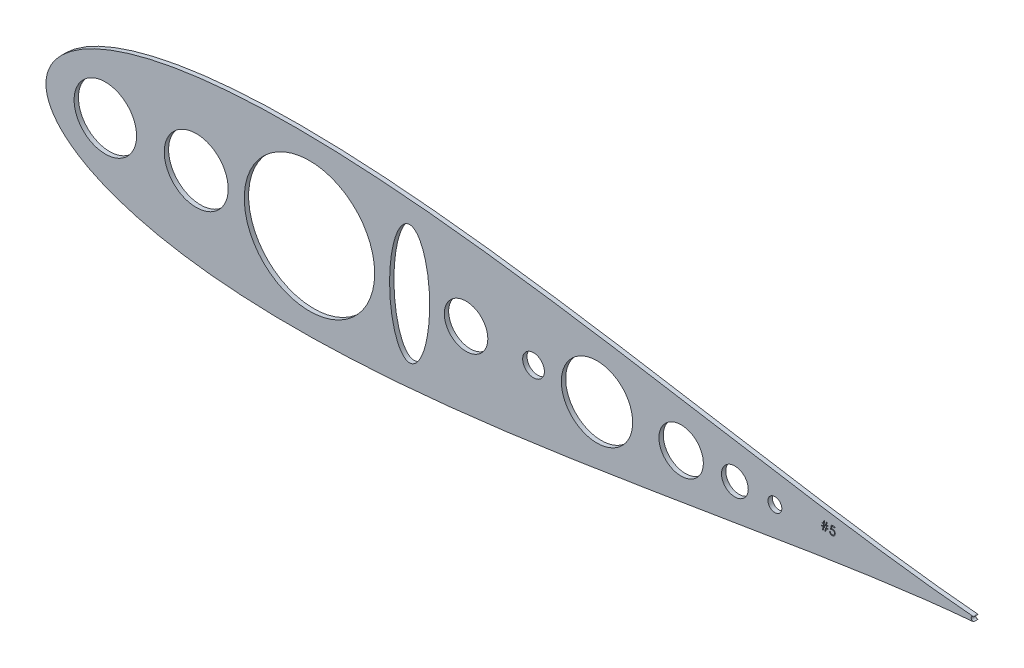
SolidWorks part; units mm, degrees
ref_plane "Front Plane" through (0, 0, 0) normal (0, 0, 1) x (1, 0, 0)
ref_plane "Top Plane" through (0, 0, 0) normal (0, 1, 0) x (1, 0, 0)
ref_plane "Right Plane" through (0, 0, 0) normal (1, 0, 0) x (0, 0, -1)
sketch "Model" plane through (0, 0, 0) normal (0, 0, 1) x (1, 0, 0)
  line L0 (738.2935, 524.3398) -> (738.2935, 524.0142)
  line L1 (738.2935, 524.0142) -> (737.3226, 524.0142)
  line L2 (737.3226, 524.0142) -> (737.0591, 522.2557)
  line L3 (737.0591, 522.2557) -> (736.6653, 522.2557)
  line L4 (736.6653, 522.2557) -> (736.9288, 524.0142)
  line L5 (736.9288, 524.0142) -> (735.8898, 524.0142)
  line L6 (735.8898, 524.0142) -> (735.6263, 522.2557)
  line L7 (735.6263, 522.2557) -> (735.2324, 522.2557)
  line L8 (735.2324, 522.2557) -> (735.496, 524.0142)
  line L9 (735.496, 524.0142) -> (734.6463, 524.0142)
  line L10 (734.6463, 524.0142) -> (734.6463, 524.3398)
  line L11 (734.6463, 524.3398) -> (735.5449, 524.3398)
  line L12 (735.5449, 524.3398) -> (735.7209, 525.5121)
  line L13 (735.7209, 525.5121) -> (734.7765, 525.5121)
  line L14 (734.7765, 525.5121) -> (734.7765, 525.8378)
  line L15 (734.7765, 525.8378) -> (735.7697, 525.8378)
  line L16 (735.7697, 525.8378) -> (736.014, 527.466)
  line L17 (736.014, 527.466) -> (736.4068, 527.466)
  line L18 (736.4068, 527.466) -> (736.1626, 525.8378)
  line L19 (736.1626, 525.8378) -> (737.2026, 525.8378)
  line L20 (737.2026, 525.8378) -> (737.4468, 527.466)
  line L21 (737.4468, 527.466) -> (737.8396, 527.466)
  line L22 (737.8396, 527.466) -> (737.5954, 525.8378)
  line L23 (737.5954, 525.8378) -> (738.4237, 525.8378)
  line L24 (738.4237, 525.8378) -> (738.4237, 525.5121)
  line L25 (738.4237, 525.5121) -> (737.5465, 525.5121)
  line L26 (737.5465, 525.5121) -> (737.3715, 524.3398)
  line L27 (737.3715, 524.3398) -> (738.2935, 524.3398)
  line L28 (737.1537, 525.5121) -> (736.1137, 525.5121)
  line L29 (736.1137, 525.5121) -> (735.9387, 524.3398)
  line L30 (735.9387, 524.3398) -> (736.9777, 524.3398)
  line L31 (736.9777, 524.3398) -> (737.1537, 525.5121)
  line L32 (742.4617, 527.3357) -> (742.4617, 526.8147)
  line L33 (742.4617, 526.8147) -> (740.7337, 526.8147)
  line L34 (740.7337, 526.8147) -> (740.46, 525.4786)
  line L35 (740.46, 525.4786) -> (740.6218, 525.5213)
  line L36 (740.6218, 525.5213) -> (740.7755, 525.5528)
  line L37 (740.7755, 525.5528) -> (740.921, 525.5712)
  line L38 (740.921, 525.5712) -> (741.0584, 525.5773)
  line L39 (741.0584, 525.5773) -> (741.2283, 525.5701)
  line L40 (741.2283, 525.5701) -> (741.3911, 525.5478)
  line L41 (741.3911, 525.5478) -> (741.5458, 525.5111)
  line L42 (741.5458, 525.5111) -> (741.6934, 525.4602)
  line L43 (741.6934, 525.4602) -> (741.8328, 525.3951)
  line L44 (741.8328, 525.3951) -> (741.9641, 525.3147)
  line L45 (741.9641, 525.3147) -> (742.0882, 525.2201)
  line L46 (742.0882, 525.2201) -> (742.2052, 525.1102)
  line L47 (742.2052, 525.1102) -> (742.3111, 524.9891)
  line L48 (742.3111, 524.9891) -> (742.4026, 524.8609)
  line L49 (742.4026, 524.8609) -> (742.481, 524.7235)
  line L50 (742.481, 524.7235) -> (742.5441, 524.579)
  line L51 (742.5441, 524.579) -> (742.594, 524.4253)
  line L52 (742.594, 524.4253) -> (742.6286, 524.2635)
  line L53 (742.6286, 524.2635) -> (742.6499, 524.0936)
  line L54 (742.6499, 524.0936) -> (742.6571, 523.9155)
  line L55 (742.6571, 523.9155) -> (742.653, 523.7913)
  line L56 (742.653, 523.7913) -> (742.6428, 523.6692)
  line L57 (742.6428, 523.6692) -> (742.6245, 523.5502)
  line L58 (742.6245, 523.5502) -> (742.5991, 523.4331)
  line L59 (742.5991, 523.4331) -> (742.5665, 523.3192)
  line L60 (742.5665, 523.3192) -> (742.5268, 523.2082)
  line L61 (742.5268, 523.2082) -> (742.479, 523.0993)
  line L62 (742.479, 523.0993) -> (742.425, 522.9925)
  line L63 (742.425, 522.9925) -> (742.365, 522.8907)
  line L64 (742.365, 522.8907) -> (742.2989, 522.7951)
  line L65 (742.2989, 522.7951) -> (742.2286, 522.7055)
  line L66 (742.2286, 522.7055) -> (742.1533, 522.6221)
  line L67 (742.1533, 522.6221) -> (742.0719, 522.5447)
  line L68 (742.0719, 522.5447) -> (741.9854, 522.4735)
  line L69 (741.9854, 522.4735) -> (741.8949, 522.4084)
  line L70 (741.8949, 522.4084) -> (741.7982, 522.3494)
  line L71 (741.7982, 522.3494) -> (741.6974, 522.2964)
  line L72 (741.6974, 522.2964) -> (741.5926, 522.2517)
  line L73 (741.5926, 522.2517) -> (741.4847, 522.213)
  line L74 (741.4847, 522.213) -> (741.3728, 522.1814)
  line L75 (741.3728, 522.1814) -> (741.2568, 522.157)
  line L76 (741.2568, 522.157) -> (741.1367, 522.1397)
  line L77 (741.1367, 522.1397) -> (741.0126, 522.1285)
  line L78 (741.0126, 522.1285) -> (740.8854, 522.1255)
  line L79 (740.8854, 522.1255) -> (740.7337, 522.1316)
  line L80 (740.7337, 522.1316) -> (740.5882, 522.1509)
  line L81 (740.5882, 522.1509) -> (740.4488, 522.1814)
  line L82 (740.4488, 522.1814) -> (740.3155, 522.2252)
  line L83 (740.3155, 522.2252) -> (740.1883, 522.2812)
  line L84 (740.1883, 522.2812) -> (740.0672, 522.3504)
  line L85 (740.0672, 522.3504) -> (739.9512, 522.4308)
  line L86 (739.9512, 522.4308) -> (739.8423, 522.5244)
  line L87 (739.8423, 522.5244) -> (739.7416, 522.6282)
  line L88 (739.7416, 522.6282) -> (739.652, 522.7391)
  line L89 (739.652, 522.7391) -> (739.5726, 522.8572)
  line L90 (739.5726, 522.8572) -> (739.5034, 522.9833)
  line L91 (739.5034, 522.9833) -> (739.4454, 523.1156)
  line L92 (739.4454, 523.1156) -> (739.3986, 523.2561)
  line L93 (739.3986, 523.2561) -> (739.362, 523.4036)
  line L94 (739.362, 523.4036) -> (739.3355, 523.5583)
  line L95 (739.3355, 523.5583) -> (739.7914, 523.5583)
  line L96 (739.7914, 523.5583) -> (739.828, 523.4138)
  line L97 (739.828, 523.4138) -> (739.8749, 523.2846)
  line L98 (739.8749, 523.2846) -> (739.9329, 523.1685)
  line L99 (739.9329, 523.1685) -> (740.001, 523.0668)
  line L100 (740.001, 523.0668) -> (740.0814, 522.9772)
  line L101 (740.0814, 522.9772) -> (740.174, 522.8968)
  line L102 (740.174, 522.8968) -> (740.2789, 522.8246)
  line L103 (740.2789, 522.8246) -> (740.3959, 522.7625)
  line L104 (740.3959, 522.7625) -> (740.52, 522.7116)
  line L105 (740.52, 522.7116) -> (740.6483, 522.676)
  line L106 (740.6483, 522.676) -> (740.7785, 522.6536)
  line L107 (740.7785, 522.6536) -> (740.9118, 522.6465)
  line L108 (740.9118, 522.6465) -> (741.0421, 522.6526)
  line L109 (741.0421, 522.6526) -> (741.1672, 522.6699)
  line L110 (741.1672, 522.6699) -> (741.2883, 522.6984)
  line L111 (741.2883, 522.6984) -> (741.4044, 522.7391)
  line L112 (741.4044, 522.7391) -> (741.5153, 522.79)
  line L113 (741.5153, 522.79) -> (741.6221, 522.8541)
  line L114 (741.6221, 522.8541) -> (741.7239, 522.9284)
  line L115 (741.7239, 522.9284) -> (741.8216, 523.0149)
  line L116 (741.8216, 523.0149) -> (741.9101, 523.1095)
  line L117 (741.9101, 523.1095) -> (741.9875, 523.2103)
  line L118 (741.9875, 523.2103) -> (742.0526, 523.3171)
  line L119 (742.0526, 523.3171) -> (742.1065, 523.4291)
  line L120 (742.1065, 523.4291) -> (742.1482, 523.5471)
  line L121 (742.1482, 523.5471) -> (742.1778, 523.6702)
  line L122 (742.1778, 523.6702) -> (742.1951, 523.7995)
  line L123 (742.1951, 523.7995) -> (742.2012, 523.9348)
  line L124 (742.2012, 523.9348) -> (742.1961, 524.0569)
  line L125 (742.1961, 524.0569) -> (742.1808, 524.1729)
  line L126 (742.1808, 524.1729) -> (742.1543, 524.2828)
  line L127 (742.1543, 524.2828) -> (742.1177, 524.3866)
  line L128 (742.1177, 524.3866) -> (742.0709, 524.4854)
  line L129 (742.0709, 524.4854) -> (742.0139, 524.578)
  line L130 (742.0139, 524.578) -> (741.9457, 524.6645)
  line L131 (741.9457, 524.6645) -> (741.8674, 524.7449)
  line L132 (741.8674, 524.7449) -> (741.7809, 524.8181)
  line L133 (741.7809, 524.8181) -> (741.6862, 524.8812)
  line L134 (741.6862, 524.8812) -> (741.5855, 524.9341)
  line L135 (741.5855, 524.9341) -> (741.4776, 524.9789)
  line L136 (741.4776, 524.9789) -> (741.3626, 525.0125)
  line L137 (741.3626, 525.0125) -> (741.2405, 525.0369)
  line L138 (741.2405, 525.0369) -> (741.1123, 525.0512)
  line L139 (741.1123, 525.0512) -> (740.9759, 525.0562)
  line L140 (740.9759, 525.0562) -> (740.8579, 525.0522)
  line L141 (740.8579, 525.0522) -> (740.7327, 525.04)
  line L142 (740.7327, 525.04) -> (740.6025, 525.0196)
  line L143 (740.6025, 525.0196) -> (740.4651, 524.9911)
  line L144 (740.4651, 524.9911) -> (740.3226, 524.9545)
  line L145 (740.3226, 524.9545) -> (740.173, 524.9097)
  line L146 (740.173, 524.9097) -> (740.0183, 524.8568)
  line L147 (740.0183, 524.8568) -> (739.8565, 524.7957)
  line L148 (739.8565, 524.7957) -> (740.3776, 527.3357)
  line L149 (740.3776, 527.3357) -> (742.4617, 527.3357)
  circle A0 centre (316.6495, 521.1085) radius 18.2309
  circle A1 centre (707.4198, 521.1085) radius 4.0377
  circle A2 centre (684.0578, 521.1085) radius 7.8218
  circle A3 centre (652.7021, 521.1085) radius 12.9578
  circle A4 centre (603.5976, 521.1085) radius 20.8135
  circle A5 centre (566.5539, 521.1085) radius 6.35
  circle A6 centre (527.1839, 521.1085) radius 12.7
  circle A7 centre (435.7938, 521.1085) radius 38.053
  circle A8 centre (369.7039, 521.1085) radius 18.669
  arc A9 (823.4212, 522.34) -> (823.4192, 519.8762) centre (823.2427, 521.1082) ccw
  arc A10 (823.4212, 522.34) -> (823.0121, 522.4406) centre (822.9014, 521.1085) ccw
  arc A11 (823.0121, 519.7764) -> (823.4192, 519.8762) centre (822.9014, 521.1085) ccw
  ellipse E0 centre (494.2426, 521.1085) end of major axis (494.2426, 486.1605) minor radius 11.7082
  spline S0 degree 3 poles (823.0121, 522.4406) (822.5764, 522.4768) (819.2929, 522.7534) (812.8264, 523.3511) (803.2279, 524.3496) (792.5858, 525.5748) (780.94, 527.0342) (768.345, 528.7291) (754.8551, 530.6559) (740.5289, 532.8045) (725.4271, 535.1596) (709.6131, 537.7002) (693.1521, 540.4001) (676.1114, 543.2282) (658.5599, 546.1488) (640.5682, 549.1221) (622.2082, 552.1052) (603.5531, 555.0523) (584.6777, 557.9153) (565.658, 560.645) (546.5712, 563.1915) (527.4962, 565.5052) (508.5129, 567.5374) (489.7028, 569.2411) (471.1488, 570.572) (452.9349, 571.4888) (435.1468, 571.9548) (417.8712, 571.9375) (401.1964, 571.4095) (385.2119, 570.3502) (370.009, 568.7441) (355.6804, 566.584) (342.3218, 563.8693) (330.032, 560.6089) (318.9148, 556.8219) (309.0813, 552.5422) (300.6507, 547.8264) (293.7491, 542.7702) (288.4927, 537.5386) (284.934, 532.4085) (282.9495, 527.78) (282.1482, 524.0671) (281.9657, 521.1085) (282.1482, 518.1499) (282.9495, 514.437) (284.934, 509.8086) (288.4927, 504.6784) (293.7491, 499.4469) (300.6507, 494.3906) (309.0813, 489.6748) (318.9148, 485.3951) (330.032, 481.6082) (342.3218, 478.3478) (355.6804, 475.633) (370.009, 473.4729) (385.2119, 471.8669) (401.1964, 470.8075) (417.8712, 470.2795) (435.1468, 470.2622) (452.9349, 470.7282) (471.1488, 471.6451) (489.7028, 472.9759) (508.5129, 474.6796) (527.4962, 476.7118) (546.5712, 479.0255) (565.658, 481.572) (584.6777, 484.3017) (603.5531, 487.1647) (622.2082, 490.1118) (640.5682, 493.0949) (658.5599, 496.0683) (676.1114, 498.9888) (693.1521, 501.8169) (709.6131, 504.5168) (725.4271, 507.0575) (740.5289, 509.4126) (754.8551, 511.5611) (768.345, 513.4879) (780.94, 515.1828) (792.5858, 516.6422) (803.2279, 517.8674) (812.8264, 518.8659) (819.2929, 519.4636) (822.5764, 519.7402) (823.0121, 519.7764) knots 0.020157 0.020157 0.020157 0.020157 0.021271 0.028553 0.036781 0.04592 0.055932 0.066773 0.078397 0.090755 0.103793 0.117456 0.131686 0.146422 0.1616 0.177156 0.193024 0.209135 0.225421 0.241812 0.258238 0.274629 0.290914 0.307025 0.322893 0.338448 0.353626 0.368361 0.38259 0.396253 0.40929 0.421647 0.43327 0.444109 0.454119 0.463255 0.471479 0.478755 0.485052 0.490344 0.49461 0.497833 0.5 0.502167 0.50539 0.509656 0.514948 0.521245 0.528521 0.536745 0.545881 0.555891 0.56673 0.578353 0.59071 0.603747 0.61741 0.631639 0.646374 0.661552 0.677107 0.692975 0.709086 0.725371 0.741762 0.758188 0.774579 0.790865 0.806976 0.822844 0.8384 0.853578 0.868314 0.882544 0.896207 0.909245 0.921603 0.933227 0.944068 0.95408 0.963219 0.971447 0.978729 0.979843 0.979843 0.979843 0.979843
sketch "Sketch2" plane through (0, 0, 0) normal (0, 0, 1) x (1, 0, 0)
  line L0 (738.2935, 524.3398) -> (738.2935, 524.0142)
  line L1 (738.2935, 524.0142) -> (737.3226, 524.0142)
  line L2 (737.3226, 524.0142) -> (737.0591, 522.2557)
  line L3 (737.0591, 522.2557) -> (736.6653, 522.2557)
  line L4 (736.6653, 522.2557) -> (736.9288, 524.0142)
  line L5 (736.9288, 524.0142) -> (735.8898, 524.0142)
  line L6 (735.8898, 524.0142) -> (735.6263, 522.2557)
  line L7 (735.6263, 522.2557) -> (735.2324, 522.2557)
  line L8 (735.2324, 522.2557) -> (735.496, 524.0142)
  line L9 (735.496, 524.0142) -> (734.6463, 524.0142)
  line L10 (734.6463, 524.0142) -> (734.6463, 524.3398)
  line L11 (734.6463, 524.3398) -> (735.5449, 524.3398)
  line L12 (735.5449, 524.3398) -> (735.7209, 525.5121)
  line L13 (735.7209, 525.5121) -> (734.7765, 525.5121)
  line L14 (734.7765, 525.5121) -> (734.7765, 525.8378)
  line L15 (734.7765, 525.8378) -> (735.7697, 525.8378)
  line L16 (735.7697, 525.8378) -> (736.014, 527.466)
  line L17 (736.014, 527.466) -> (736.4068, 527.466)
  line L18 (736.4068, 527.466) -> (736.1626, 525.8378)
  line L19 (736.1626, 525.8378) -> (737.2026, 525.8378)
  line L20 (737.2026, 525.8378) -> (737.4468, 527.466)
  line L21 (737.4468, 527.466) -> (737.8396, 527.466)
  line L22 (737.8396, 527.466) -> (737.5954, 525.8378)
  line L23 (737.5954, 525.8378) -> (738.4237, 525.8378)
  line L24 (738.4237, 525.8378) -> (738.4237, 525.5121)
  line L25 (738.4237, 525.5121) -> (737.5465, 525.5121)
  line L26 (737.5465, 525.5121) -> (737.3715, 524.3398)
  line L27 (737.3715, 524.3398) -> (738.2935, 524.3398)
  line L28 (737.1537, 525.5121) -> (736.1137, 525.5121)
  line L29 (736.1137, 525.5121) -> (735.9387, 524.3398)
  line L30 (735.9387, 524.3398) -> (736.9777, 524.3398)
  line L31 (736.9777, 524.3398) -> (737.1537, 525.5121)
  line L32 (742.4617, 527.3357) -> (742.4617, 526.8147)
  line L33 (742.4617, 526.8147) -> (740.7337, 526.8147)
  line L34 (740.7337, 526.8147) -> (740.46, 525.4786)
  line L35 (740.46, 525.4786) -> (740.6218, 525.5213)
  line L36 (740.6218, 525.5213) -> (740.7755, 525.5528)
  line L37 (740.7755, 525.5528) -> (740.921, 525.5712)
  line L38 (740.921, 525.5712) -> (741.0584, 525.5773)
  line L39 (741.0584, 525.5773) -> (741.2283, 525.5701)
  line L40 (741.2283, 525.5701) -> (741.3911, 525.5478)
  line L41 (741.3911, 525.5478) -> (741.5458, 525.5111)
  line L42 (741.5458, 525.5111) -> (741.6934, 525.4602)
  line L43 (741.6934, 525.4602) -> (741.8328, 525.3951)
  line L44 (741.8328, 525.3951) -> (741.9641, 525.3147)
  line L45 (741.9641, 525.3147) -> (742.0882, 525.2201)
  line L46 (742.0882, 525.2201) -> (742.2052, 525.1102)
  line L47 (742.2052, 525.1102) -> (742.3111, 524.9891)
  line L48 (742.3111, 524.9891) -> (742.4026, 524.8609)
  line L49 (742.4026, 524.8609) -> (742.481, 524.7235)
  line L50 (742.481, 524.7235) -> (742.5441, 524.579)
  line L51 (742.5441, 524.579) -> (742.594, 524.4253)
  line L52 (742.594, 524.4253) -> (742.6286, 524.2635)
  line L53 (742.6286, 524.2635) -> (742.6499, 524.0936)
  line L54 (742.6499, 524.0936) -> (742.6571, 523.9155)
  line L55 (742.6571, 523.9155) -> (742.653, 523.7913)
  line L56 (742.653, 523.7913) -> (742.6428, 523.6692)
  line L57 (742.6428, 523.6692) -> (742.6245, 523.5502)
  line L58 (742.6245, 523.5502) -> (742.5991, 523.4331)
  line L59 (742.5991, 523.4331) -> (742.5665, 523.3192)
  line L60 (742.5665, 523.3192) -> (742.5268, 523.2082)
  line L61 (742.5268, 523.2082) -> (742.479, 523.0993)
  line L62 (742.479, 523.0993) -> (742.425, 522.9925)
  line L63 (742.425, 522.9925) -> (742.365, 522.8907)
  line L64 (742.365, 522.8907) -> (742.2989, 522.7951)
  line L65 (742.2989, 522.7951) -> (742.2286, 522.7055)
  line L66 (742.2286, 522.7055) -> (742.1533, 522.6221)
  line L67 (742.1533, 522.6221) -> (742.0719, 522.5447)
  line L68 (742.0719, 522.5447) -> (741.9854, 522.4735)
  line L69 (741.9854, 522.4735) -> (741.8949, 522.4084)
  line L70 (741.8949, 522.4084) -> (741.7982, 522.3494)
  line L71 (741.7982, 522.3494) -> (741.6974, 522.2964)
  line L72 (741.6974, 522.2964) -> (741.5926, 522.2517)
  line L73 (741.5926, 522.2517) -> (741.4847, 522.213)
  line L74 (741.4847, 522.213) -> (741.3728, 522.1814)
  line L75 (741.3728, 522.1814) -> (741.2568, 522.157)
  line L76 (741.2568, 522.157) -> (741.1367, 522.1397)
  line L77 (741.1367, 522.1397) -> (741.0126, 522.1285)
  line L78 (741.0126, 522.1285) -> (740.8854, 522.1255)
  line L79 (740.8854, 522.1255) -> (740.7337, 522.1316)
  line L80 (740.7337, 522.1316) -> (740.5882, 522.1509)
  line L81 (740.5882, 522.1509) -> (740.4488, 522.1814)
  line L82 (740.4488, 522.1814) -> (740.3155, 522.2252)
  line L83 (740.3155, 522.2252) -> (740.1883, 522.2812)
  line L84 (740.1883, 522.2812) -> (740.0672, 522.3504)
  line L85 (740.0672, 522.3504) -> (739.9512, 522.4308)
  line L86 (739.9512, 522.4308) -> (739.8423, 522.5244)
  line L87 (739.8423, 522.5244) -> (739.7416, 522.6282)
  line L88 (739.7416, 522.6282) -> (739.652, 522.7391)
  line L89 (739.652, 522.7391) -> (739.5726, 522.8572)
  line L90 (739.5726, 522.8572) -> (739.5034, 522.9833)
  line L91 (739.5034, 522.9833) -> (739.4454, 523.1156)
  line L92 (739.4454, 523.1156) -> (739.3986, 523.2561)
  line L93 (739.3986, 523.2561) -> (739.362, 523.4036)
  line L94 (739.362, 523.4036) -> (739.3355, 523.5583)
  line L95 (739.3355, 523.5583) -> (739.7914, 523.5583)
  line L96 (739.7914, 523.5583) -> (739.828, 523.4138)
  line L97 (739.828, 523.4138) -> (739.8749, 523.2846)
  line L98 (739.8749, 523.2846) -> (739.9329, 523.1685)
  line L99 (739.9329, 523.1685) -> (740.001, 523.0668)
  line L100 (740.001, 523.0668) -> (740.0814, 522.9772)
  line L101 (740.0814, 522.9772) -> (740.174, 522.8968)
  line L102 (740.174, 522.8968) -> (740.2789, 522.8246)
  line L103 (740.2789, 522.8246) -> (740.3959, 522.7625)
  line L104 (740.3959, 522.7625) -> (740.52, 522.7116)
  line L105 (740.52, 522.7116) -> (740.6483, 522.676)
  line L106 (740.6483, 522.676) -> (740.7785, 522.6536)
  line L107 (740.7785, 522.6536) -> (740.9118, 522.6465)
  line L108 (740.9118, 522.6465) -> (741.0421, 522.6526)
  line L109 (741.0421, 522.6526) -> (741.1672, 522.6699)
  line L110 (741.1672, 522.6699) -> (741.2883, 522.6984)
  line L111 (741.2883, 522.6984) -> (741.4044, 522.7391)
  line L112 (741.4044, 522.7391) -> (741.5153, 522.79)
  line L113 (741.5153, 522.79) -> (741.6221, 522.8541)
  line L114 (741.6221, 522.8541) -> (741.7239, 522.9284)
  line L115 (741.7239, 522.9284) -> (741.8216, 523.0149)
  line L116 (741.8216, 523.0149) -> (741.9101, 523.1095)
  line L117 (741.9101, 523.1095) -> (741.9875, 523.2103)
  line L118 (741.9875, 523.2103) -> (742.0526, 523.3171)
  line L119 (742.0526, 523.3171) -> (742.1065, 523.4291)
  line L120 (742.1065, 523.4291) -> (742.1482, 523.5471)
  line L121 (742.1482, 523.5471) -> (742.1778, 523.6702)
  line L122 (742.1778, 523.6702) -> (742.1951, 523.7995)
  line L123 (742.1951, 523.7995) -> (742.2012, 523.9348)
  line L124 (742.2012, 523.9348) -> (742.1961, 524.0569)
  line L125 (742.1961, 524.0569) -> (742.1808, 524.1729)
  line L126 (742.1808, 524.1729) -> (742.1543, 524.2828)
  line L127 (742.1543, 524.2828) -> (742.1177, 524.3866)
  line L128 (742.1177, 524.3866) -> (742.0709, 524.4854)
  line L129 (742.0709, 524.4854) -> (742.0139, 524.578)
  line L130 (742.0139, 524.578) -> (741.9457, 524.6645)
  line L131 (741.9457, 524.6645) -> (741.8674, 524.7449)
  line L132 (741.8674, 524.7449) -> (741.7809, 524.8181)
  line L133 (741.7809, 524.8181) -> (741.6862, 524.8812)
  line L134 (741.6862, 524.8812) -> (741.5855, 524.9341)
  line L135 (741.5855, 524.9341) -> (741.4776, 524.9789)
  line L136 (741.4776, 524.9789) -> (741.3626, 525.0125)
  line L137 (741.3626, 525.0125) -> (741.2405, 525.0369)
  line L138 (741.2405, 525.0369) -> (741.1123, 525.0512)
  line L139 (741.1123, 525.0512) -> (740.9759, 525.0562)
  line L140 (740.9759, 525.0562) -> (740.8579, 525.0522)
  line L141 (740.8579, 525.0522) -> (740.7327, 525.04)
  line L142 (740.7327, 525.04) -> (740.6025, 525.0196)
  line L143 (740.6025, 525.0196) -> (740.4651, 524.9911)
  line L144 (740.4651, 524.9911) -> (740.3226, 524.9545)
  line L145 (740.3226, 524.9545) -> (740.173, 524.9097)
  line L146 (740.173, 524.9097) -> (740.0183, 524.8568)
  line L147 (740.0183, 524.8568) -> (739.8565, 524.7957)
  line L148 (739.8565, 524.7957) -> (740.3776, 527.3357)
  line L149 (740.3776, 527.3357) -> (742.4617, 527.3357)
  line L150 (282.018, 521.1085) -> (298.4187, 521.1085)
  line L151 (282.018, 521.1085) -> (298.4187, 521.1085) construction
  circle A0 centre (316.6495, 521.1085) radius 18.2309
  circle A1 centre (707.4198, 521.1085) radius 4.0377
  circle A2 centre (684.0578, 521.1085) radius 7.8218
  circle A3 centre (652.7021, 521.1085) radius 12.9578
  circle A4 centre (603.5976, 521.1085) radius 20.8135
  circle A5 centre (566.5539, 521.1085) radius 6.35
  circle A6 centre (527.1839, 521.1085) radius 12.7
  circle A7 centre (435.7938, 521.1085) radius 38.053
  circle A8 centre (369.7039, 521.1085) radius 18.669
  arc A9 (823.4212, 522.34) -> (823.4192, 519.8762) centre (823.2427, 521.1082) ccw
  arc A10 (823.4212, 522.34) -> (823.0121, 522.4406) centre (822.9014, 521.1085) ccw
  arc A11 (823.0121, 519.7764) -> (823.4192, 519.8762) centre (822.9014, 521.1085) ccw
  ellipse E0 centre (494.2426, 521.1085) end of major axis (494.2426, 486.1605) minor radius 11.7082
  spline S0 degree 3 poles (823.0121, 522.4406) (822.5764, 522.4768) (819.2929, 522.7534) (812.8264, 523.3511) (803.2279, 524.3496) (792.5858, 525.5748) (780.94, 527.0342) (768.345, 528.7291) (754.8551, 530.6559) (740.5289, 532.8045) (725.4271, 535.1596) (709.6131, 537.7002) (693.1521, 540.4001) (676.1114, 543.2282) (658.5599, 546.1488) (640.5682, 549.1221) (622.2082, 552.1052) (603.5531, 555.0523) (584.6777, 557.9153) (565.658, 560.645) (546.5712, 563.1915) (527.4962, 565.5052) (508.5129, 567.5374) (489.7028, 569.2411) (471.1488, 570.572) (452.9349, 571.4888) (435.1468, 571.9548) (417.8712, 571.9375) (401.1964, 571.4095) (385.2119, 570.3502) (370.009, 568.7441) (355.6804, 566.584) (342.3218, 563.8693) (330.032, 560.6089) (318.9148, 556.8219) (309.0813, 552.5422) (300.6507, 547.8264) (293.7491, 542.7702) (288.4927, 537.5386) (284.934, 532.4085) (282.9495, 527.78) (282.1482, 524.0671) (281.9657, 521.1085) (282.1482, 518.1499) (282.9495, 514.437) (284.934, 509.8086) (288.4927, 504.6784) (293.7491, 499.4469) (300.6507, 494.3906) (309.0813, 489.6748) (318.9148, 485.3951) (330.032, 481.6082) (342.3218, 478.3478) (355.6804, 475.633) (370.009, 473.4729) (385.2119, 471.8669) (401.1964, 470.8075) (417.8712, 470.2795) (435.1468, 470.2622) (452.9349, 470.7282) (471.1488, 471.6451) (489.7028, 472.9759) (508.5129, 474.6796) (527.4962, 476.7118) (546.5712, 479.0255) (565.658, 481.572) (584.6777, 484.3017) (603.5531, 487.1647) (622.2082, 490.1118) (640.5682, 493.0949) (658.5599, 496.0683) (676.1114, 498.9888) (693.1521, 501.8169) (709.6131, 504.5168) (725.4271, 507.0575) (740.5289, 509.4126) (754.8551, 511.5611) (768.345, 513.4879) (780.94, 515.1828) (792.5858, 516.6422) (803.2279, 517.8674) (812.8264, 518.8659) (819.2929, 519.4636) (822.5764, 519.7402) (823.0121, 519.7764) knots 0.020157 0.020157 0.020157 0.020157 0.021271 0.028553 0.036781 0.04592 0.055932 0.066773 0.078397 0.090755 0.103793 0.117456 0.131686 0.146422 0.1616 0.177156 0.193024 0.209135 0.225421 0.241812 0.258238 0.274629 0.290914 0.307025 0.322893 0.338448 0.353626 0.368361 0.38259 0.396253 0.40929 0.421647 0.43327 0.444109 0.454119 0.463255 0.471479 0.478755 0.485052 0.490344 0.49461 0.497833 0.5 0.502167 0.50539 0.509656 0.514948 0.521245 0.528521 0.536745 0.545881 0.555891 0.56673 0.578353 0.59071 0.603747 0.61741 0.631639 0.646374 0.661552 0.677107 0.692975 0.709086 0.725371 0.741762 0.758188 0.774579 0.790865 0.806976 0.822844 0.8384 0.853578 0.868314 0.882544 0.896207 0.909245 0.921603 0.933227 0.944068 0.95408 0.963219 0.971447 0.978729 0.979843 0.979843 0.979843 0.979843
extrude "Boss-Extrude1" add sketch "Sketch2" along normal blind 2.54 contours A10 S0 A11 A9 L148 L149 L32 L33 L34 L35 L36 L37 L38 L39 L40 L41 L42 L43 L44 L45 L46 L47 L48 L49 L50 L51 L52 L53 L54 L55 L56 L57 L58 L59 L60 L61 L62 L63 L64 L65 L66 L67 L68 L69 L70 L71 L72 L73 L74 L75
